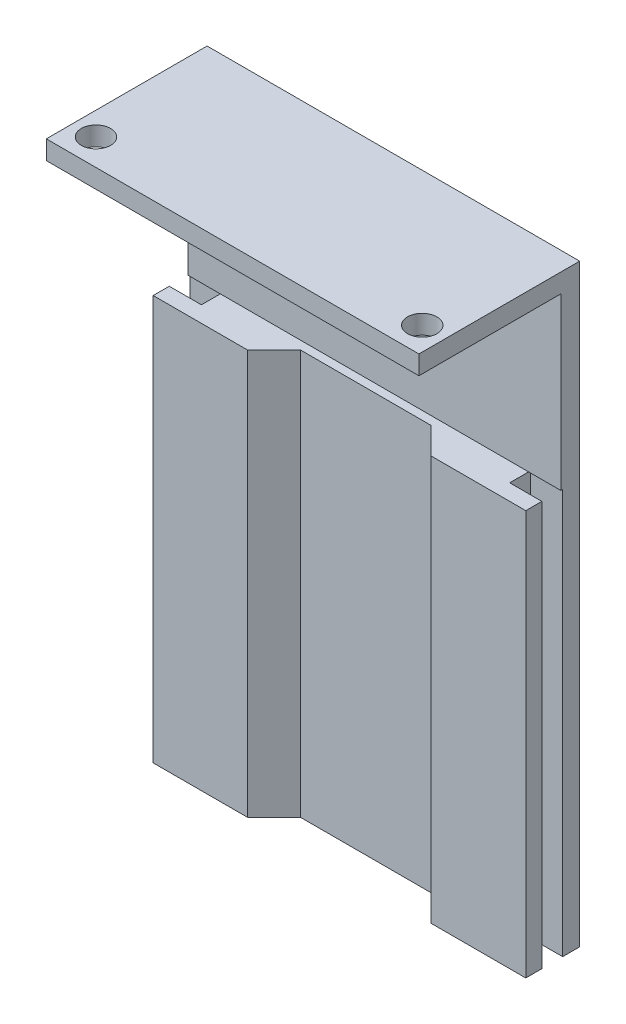
SolidWorks part; units mm, degrees
ref_plane "Plano frontal" through (0, 0, 0) normal (0, 0, 1) x (1, 0, 0)
ref_plane "Plano superior" through (0, 0, 0) normal (0, 1, 0) x (1, 0, 0)
ref_plane "Plano direito" through (0, 0, 0) normal (1, 0, 0) x (0, 0, -1)
sketch "Esboço1" plane through (0, 0, 0) normal (0, 1, 0) x (1, 0, 0)
  line L0 (-20, 2.9) -> (20, 2.9)
  line L1 (20, 2.9) -> (20, 0.9)
  line L2 (20, 0.9) -> (16.5, 0.9)
  line L3 (16.5, 0.9) -> (16.5, -0.9)
  line L4 (16.5, -0.9) -> (20, -0.9)
  line L5 (20, -0.9) -> (20, -2.9)
  line L6 (20, -2.9) -> (-20, -2.9)
  line L7 (-20, -2.9) -> (-20, -0.9)
  line L8 (-20, -0.9) -> (-16.5, -0.9)
  line L9 (-16.5, -0.9) -> (-16.5, 0.9)
  line L10 (-16.5, 0.9) -> (-20, 0.9)
  line L11 (-20, 0.9) -> (-20, 2.9)
extrude "Ressalto-extrusão1" add sketch "Esboço1" along normal blind 63
sketch "Esboço2" plane through (20, 0, 0) normal (1, 0, 0) x (0, 0, -1)
  line L0 (0.9, 63) -> (0.9, 0) construction
  line L1 (-2.9, 63) -> (0.9, 63)
  line L2 (-2.9, 63) -> (-2.9, 43)
  line L3 (-2.9, 43) -> (0.9, 43)
  line L4 (0.9, 63) -> (0.9, 43)
  dimension "D1" = 20
extrude "Corte-extrusão1" cut sketch "Esboço2" against normal through all
sketch "Esboço3" plane through (0, 0, -0.9) normal (0, 0, 1) x (1, 0, 0)
  line L0 (20, 63) -> (20, 0) construction
  line L1 (-20, 63) -> (20, 63)
  line L2 (-20, 63) -> (-20, 61)
  line L3 (-20, 61) -> (20, 61)
  line L4 (20, 63) -> (20, 61)
  dimension "D1" = 2
extrude "Ressalto-extrusão2" add sketch "Esboço3" along normal blind 15
sketch "Esboço4" plane through (0, 63, 0) normal (0, 1, 0) x (1, 0, 0)
  line L0 (-20, -14.1) -> (-17.25, -14.1) construction
  line L1 (20, -14.1) -> (-20, -14.1) construction
  line L2 (-17.25, -14.1) -> (-17.25, -11.3) construction
  line L3 (20, -14.1) -> (17.25, -14.1) construction
  line L4 (17.25, -14.1) -> (17.25, -11.3) construction
  circle A0 centre (-17.25, -11.3) radius 1.55
  circle A1 centre (17.25, -11.3) radius 1.55
  dimension "D3" = 3.1
  dimension "D6" = 3.1
  dimension "D1" = 2.75
  dimension "D2" = 2.8
  dimension "D4" = 2.75
  dimension "D5" = 2.8
extrude "Corte-extrusão2" cut sketch "Esboço4" against normal blind 3
sketch "Esboço5" plane through (0, 0, 0) normal (0, -1, 0) x (1, 0, 0)
  line L0 (20, -2.9) -> (-20, -2.9) construction
  line L1 (-20, 14.1) -> (-19.7, 14.1)
  line L2 (-20, 14.1) -> (-20, -2.9)
  line L3 (-20, -2.9) -> (-19.7, -2.9)
  line L4 (-19.7, 14.1) -> (-19.7, -2.9)
  line L6 (20, 14.1) -> (19.7, 14.1)
  line L7 (20, 14.1) -> (20, -2.9)
  line L8 (20, -2.9) -> (19.7, -2.9)
  line L9 (19.7, 14.1) -> (19.7, -2.9)
  dimension "D1" = 0.3
  dimension "D2" = 0.3
extrude "Corte-extrusão3" cut sketch "Esboço5" against normal through all
sketch "Esboço6" plane through (0, 0, 0) normal (0, -1, 0) x (1, 0, 0)
  line L0 (19.7, 0.9) -> (16.5, -0.9) construction
  line L1 (16.5, -0.9) -> (16.5, 0.9) construction
  line L2 (16.5, 0.9) -> (19.7, -0.9) construction
  line L3 (-19.7, 0.9) -> (-16.5, -0.9) construction
  line L4 (19.9, 1.1) -> (16.3, 1.1)
  line L5 (19.9, 1.1) -> (19.9, -1.1)
  line L6 (19.9, -1.1) -> (16.3, -1.1)
  line L7 (16.3, 1.1) -> (16.3, -1.1)
  line L8 (19.9, 1.1) -> (16.3, -1.1) construction
  line L9 (19.9, -1.1) -> (16.3, 1.1) construction
  line L10 (-16.5, -0.9) -> (-16.5, 0.9) construction
  line L11 (-16.5, 0.9) -> (-19.7, -0.9) construction
  line L13 (-16.3, 1.1) -> (-19.9, 1.1)
  line L14 (-16.3, 1.1) -> (-16.3, -1.1)
  line L15 (-16.3, -1.1) -> (-19.9, -1.1)
  line L16 (-19.9, 1.1) -> (-19.9, -1.1)
  line L17 (-16.3, 1.1) -> (-19.9, -1.1) construction
  line L18 (-16.3, -1.1) -> (-19.9, 1.1) construction
  point P4 (18.1, 0)
  point P17 (-18.1, 0)
  dimension "D1" = 3.6
  dimension "D2" = 3.6
  dimension "D3" = 2.2
  dimension "D4" = 2.2
extrude "Corte-extrusão4" cut sketch "Esboço6" against normal blind 43
sketch "Esboço7" plane through (0, 0, 0) normal (0, -1, 0) x (1, 0, 0)
  line L0 (-19.7, 1.1) -> (-19.7, 2.9) construction
  line L1 (19.7, 2.9) -> (-19.7, 2.9)
  line L2 (19.7, 2.9) -> (19.7, 2.8)
  line L3 (19.7, 2.8) -> (-19.7, 2.8)
  line L4 (-19.7, 2.9) -> (-19.7, 2.8)
  dimension "D1" = 0.1
extrude "Corte-extrusão5" cut sketch "Esboço7" against normal blind 46
sketch "Esboço8" plane through (0, 0, 0) normal (0, -1, 0) x (1, 0, 0)
  line L0 (0, 0) -> (16.3, 0) construction
  line L1 (16.3, 1.1) -> (16.3, -1.1) construction
  line L2 (16.3, 0) -> (-16.3, 0) construction
  line L3 (-16.3, -1.1) -> (-16.3, 1.1) construction
  line L4 (-19.7, 2.8) -> (-9.7, 2.8) construction
  line L5 (-19.7, 2.8) -> (19.7, 2.8) construction
  line L6 (19.7, 2.8) -> (9.7, 2.8) construction
  line L7 (9.7, 2.8) -> (6.9, 0)
  line L8 (6.9, 0) -> (-6.1357, 0)
  line L9 (-9.7, 2.8) -> (-6.9, 0)
  line L10 (-6.9, 0) -> (-6.1357, 0)
  line L11 (9.7, 2.8) -> (-9.7, 2.8)
  dimension "D1" = 10
  dimension "D2" = 10
extrude "Corte-extrusão6" cut sketch "Esboço8" against normal blind 43
sketch "Esboço9" plane through (0, 0, 2.8) normal (0, 0, 1) x (1, 0, 0)
  line L0 (-19.7, 0) -> (-19.7, 43) construction
  line L1 (19.7, 0) -> (-19.7, 0)
  line L2 (19.7, 0) -> (19.7, 0.2)
  line L3 (19.7, 0.2) -> (-19.7, 0.2)
  line L4 (-19.7, 0) -> (-19.7, 0.2)
  dimension "D1" = 0.2
extrude "Corte-extrusão7" cut sketch "Esboço9" against normal blind 10
